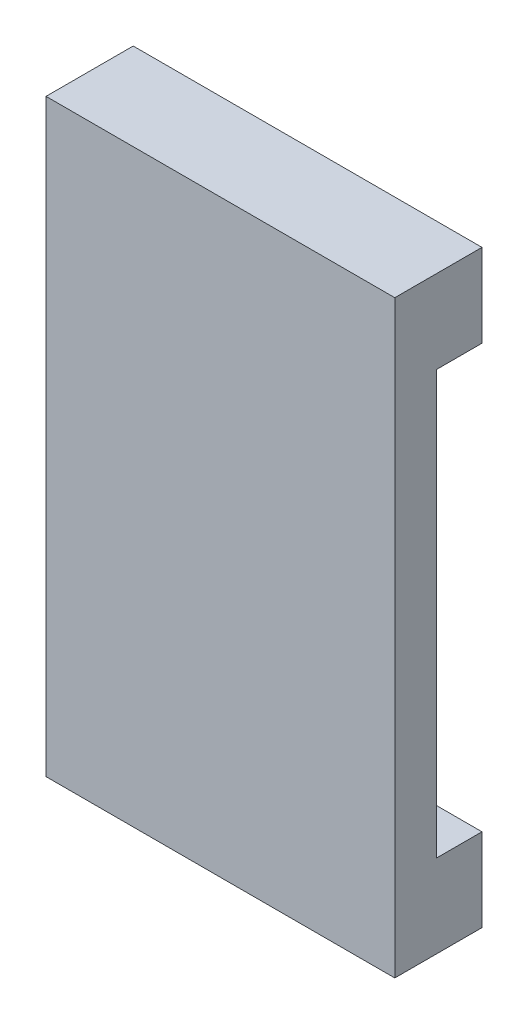
SolidWorks part; units mm, degrees
ref_plane "Alzado" through (0, 0, 0) normal (0, 0, 1) x (1, 0, 0)
ref_plane "Planta" through (0, 0, 0) normal (0, 1, 0) x (1, 0, 0)
ref_plane "Vista lateral" through (0, 0, 0) normal (1, 0, 0) x (0, 0, -1)
sketch "Croquis1" plane through (0, 0, 0) normal (0, 0, 1) x (1, 0, 0)
  line L0 (55, 0) -> (-55, 0) construction
  line L1 (-16, 25.515) -> (16, 25.515)
  line L2 (-16, 25.515) -> (-16, -25.435)
  line L3 (-16, -25.435) -> (16, -25.435)
  line L4 (16, 25.515) -> (16, -25.435)
  line L5 (0, -55) -> (0, 55) construction
  line L7 (-26, -35.435) -> (16, -35.435)
  line L8 (-26, -35.435) -> (-26, 35.515)
  line L9 (-26, 35.515) -> (16, 35.515)
  line L10 (16, -35.435) -> (16, 35.515)
  line L11 (-8, 21.608) -> (-2, 21.608)
  line L12 (-8, 21.608) -> (-8, 17.568)
  line L13 (-8, 17.568) -> (-2, 17.568)
  line L14 (-2, 21.608) -> (-2, 17.568)
  line L15 (-8, -17.488) -> (-2, -17.488)
  line L16 (-8, -17.488) -> (-8, -21.528)
  line L17 (-8, -21.528) -> (-2, -21.528)
  line L18 (-2, -17.488) -> (-2, -21.528)
  dimension "D1" = 32
  dimension "D2" = 50.95
  dimension "D3" = 25.515
  dimension "D4" = 16
  dimension "D5" = 10
  dimension "D6" = 10
  dimension "D7" = 10
  dimension "D8" = 0
  dimension "D9" = 4.04
  dimension "D10" = 8
  dimension "D11" = 6
  dimension "D12" = 3.907
  dimension "D13" = 3.907
  dimension "D14" = 8
  dimension "D15" = 6
  dimension "D16" = 4.04
extrude "Saliente-Extruir1" add sketch "Croquis1" along normal blind 5.5 contours L7 L10 L3 L2 L1 L9 L8 | L14 L13 L12 L11
sketch "Croquis2" plane through (0, 0, 5.5) normal (0, 0, 1) x (1, 0, 0)
  line L1 (-26, 35.515) -> (16, 35.515)
  line L2 (-26, 35.515) -> (-26, -35.435)
  line L3 (-26, -35.435) -> (16, -35.435)
  line L4 (16, 35.515) -> (16, -35.435)
extrude "Saliente-Extruir2" add sketch "Croquis2" along normal blind 5
